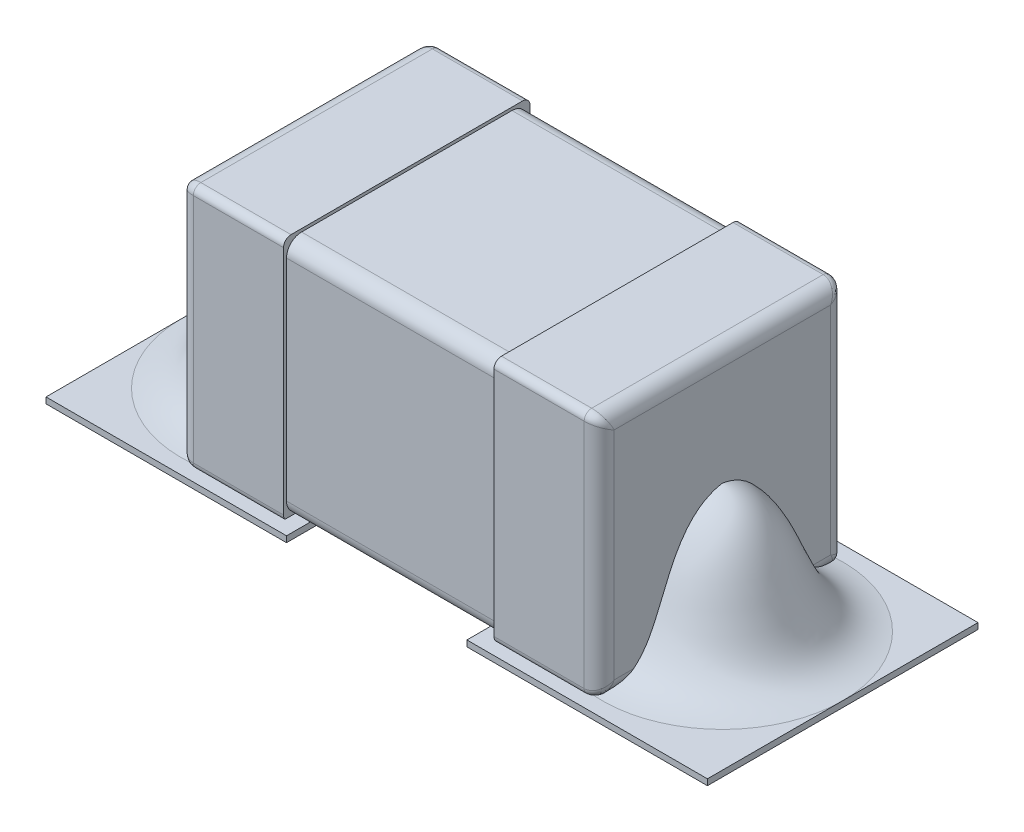
SolidWorks part; units mm, degrees
ref_plane "Alzado" through (0, 0, 0) normal (0, 0, 1) x (1, 0, 0)
ref_plane "Planta" through (0, 0, 0) normal (0, 1, 0) x (1, 0, 0)
ref_plane "Vista lateral" through (0, 0, 0) normal (1, 0, 0) x (0, 0, -1)
sketch "Croquis1" plane through (0, 0, 0) normal (0, 1, 0) x (1, 0, 0)
  line L1 (-0.35, -0.4) -> (0.35, -0.4)
  line L2 (-0.35, -0.4) -> (-0.35, 0.4)
  line L3 (-0.35, 0.4) -> (0.35, 0.4)
  line L4 (0.35, -0.4) -> (0.35, 0.4)
  line L5 (-0.35, -0.4) -> (0.35, 0.4) construction
  line L6 (-0.35, 0.4) -> (0.35, -0.4) construction
  point P0 (0, 0)
  dimension "D1" = 0.7
  dimension "D2" = 0.8
extrude "Saliente-Extruir1" add sketch "Croquis1" along normal blind 0.8
sketch "Croquis2" plane through (0.35, 0, 0) normal (1, 0, 0) x (0, 0, -1)
  line L0 (-0.4, 0.8) -> (-0.4, 0) construction
  line L1 (-0.41, -0.01) -> (0.41, -0.01)
  line L2 (-0.41, -0.01) -> (-0.41, 0.81)
  line L3 (-0.41, 0.81) -> (0.41, 0.81)
  line L4 (0.41, -0.01) -> (0.41, 0.81)
  line L5 (-0.4, 0.8) -> (0.4, 0.8) construction
  dimension "D1" = 0.82
  dimension "D2" = 0.82
  dimension "D3" = 0.01
  dimension "D4" = 0.01
extrude "Saliente-Extruir3" add sketch "Croquis2" along normal blind 0.35 separate body
fillet "Redondeo2" radius 0.05 4 edges at (0, 0, -0.4) (0, 0, 0.4) (0, 0.8, -0.4) (0, 0.8, 0.4)
fillet "Redondeo1" radius 0.05 4 edges at (0.7, 0.4, -0.41) (0.7, -0.01, 0) (0.7, 0.4, 0.41) (0.7, 0.81, 0)
fillet "Redondeo3" radius 0.025 8 edges at (0.6854, 0.0046, 0.3954) (0.6854, 0.0046, -0.3954) (0.6854, 0.7954, 0.3954) (0.6854, 0.7954, -0.3954) (0.5, -0.01, 0.41) (0.5, -0.01, -0.41) (0.5, 0.81, 0.41) (0.5, 0.81, -0.41)
mirror "Simetría3" about plane through (0, 0, 0) normal (1, 0, 0) of bodies 103
sketch "Croquis3" plane through (0, 0, 0) normal (0, 1, 0) x (1, 0, 0)
  line L0 (-0.35, 0.4) -> (0.35, 0.4) construction
  line L1 (0.3, -0.45) -> (1.1, -0.45)
  line L2 (0.3, -0.45) -> (0.3, 0.45)
  line L3 (0.3, 0.45) -> (1.1, 0.45)
  line L4 (1.1, -0.45) -> (1.1, 0.45)
  line L7 (0.35, -0.35) -> (0.35, 0.35) construction
  dimension "D1" = 0.9
  dimension "D2" = 0.05
  dimension "D3" = 0.8
  dimension "D4" = 0.05
extrude "Saliente-Extruir4" add sketch "Croquis3" against normal blind 0.02
mirror "Simetría4" about plane through (0, 0, 0) normal (1, 0, 0) of "Saliente-Extruir4"
sketch "Croquis4" plane through (0, 0, 0) normal (0, 0, 1) x (1, 0, 0)
  line L0 (0.7, 0.76) -> (0.7, 0.04) construction
  line L3 (1.1, 0) -> (0.9475, 0.0231) construction
  line L4 (0.9475, 0.0231) -> (0.9026, 0.0999) construction
  line L5 (0.9026, 0.0999) -> (0.9005, 0.393) construction
  line L6 (0.9005, 0.393) -> (0.7, 0.4268) construction
  line L7 (0.7, 0.4268) -> (0.7, 0)
  line L8 (0.3, 0) -> (1.1, 0) construction
  line L9 (0.7, 0) -> (1.1, 0)
  spline S0 degree 4 poles (1.1, 0) (0.9475, 0.0231) (0.9026, 0.0999) (0.9005, 0.393) (0.7, 0.4268) knots 0 0 0 0 0 1 1 1 1 1
revolve "Revolución1" add sketch "Croquis4" angle 360 about L7
mirror "Simetría5" about plane through (0, 0, 0) normal (1, 0, 0) of "Revolución1"
